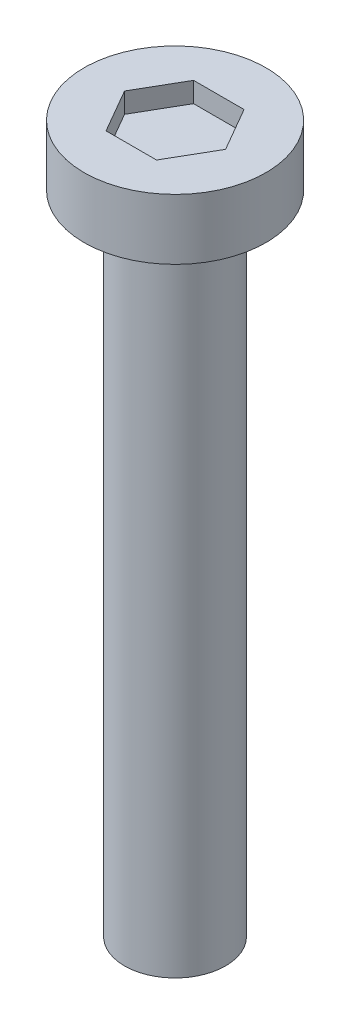
SolidWorks part; units mm, degrees
ref_plane "Front Plane" through (0, 0, 0) normal (0, 0, 1) x (1, 0, 0)
ref_plane "Top Plane" through (0, 0, 0) normal (0, 1, 0) x (1, 0, 0)
ref_plane "Right Plane" through (0, 0, 0) normal (1, 0, 0) x (0, 0, -1)
sketch "Sketch1" plane through (0, 0, 0) normal (0, 1, 0) x (1, 0, 0)
  circle A0 centre (0, 0) radius 1.25
  dimension "D1" = 2.5
extrude "Boss-Extrude1" add sketch "Sketch1" along normal blind 16
sketch "Sketch4" plane through (0, 16, 0) normal (0, 1, 0) x (1, 0, 0)
  circle A0 centre (0, 0) radius 2.25
  dimension "D1" = 4.5
extrude "Boss-Extrude2" add sketch "Sketch4" along normal blind 1.5
sketch "Sketch5" plane through (0, 17.5, 0) normal (0, 1, 0) x (1, 0, 0)
  line L1 (1.25, 0) -> (0.625, 1.0825)
  line L2 (0.625, 1.0825) -> (-0.625, 1.0825)
  line L3 (-0.625, 1.0825) -> (-1.25, 0)
  line L4 (-1.25, 0) -> (-0.625, -1.0825)
  line L5 (-0.625, -1.0825) -> (0.625, -1.0825)
  line L6 (0.625, -1.0825) -> (1.25, 0)
  circle A0 centre (0, 0) radius 1.0825 construction
  dimension "D1" = 1.25
extrude "Cut-Extrude1" cut sketch "Sketch5" against normal blind 0.5
thread "Thread1" pitch 0.7 start angle 0, offset 0, length 14, pitch 0.7, diameter 2.5
ref_plane "Plane1" through (1.25, 0, 0) normal (0, 0, 1) x (1, 0, 0)
sketch "Thread Profile1" plane through (1.25, 0, 0) normal (0, 0, 1) x (1, 0, 0)
  line L0 (0, 0) -> (0, 0.7) construction
  line L1 (0, 0) -> (0.3789, 0.2187)
  line L2 (0.3789, 0.2187) -> (0.3789, 0.3062)
  line L3 (0.3789, 0.3062) -> (0, 0.525)
  line L4 (0.3789, 0.2625) -> (0, 0.2625) construction
  line L11 (0, 0) -> (0, 0.525)
  point P2 (0, 0)
  dimension "Pitch" = 0.7
  dimension "Profile_Angle" = 60
  dimension "Profile_Land" = 0.0875
  dimension "Profile_Height" = 0.3789
